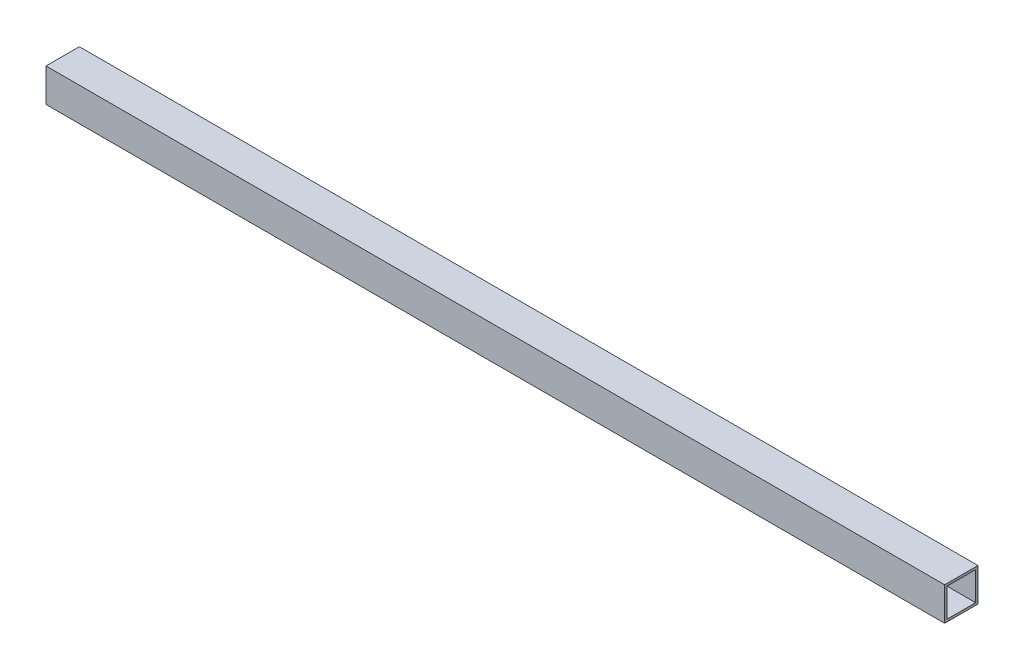
SolidWorks part; units mm, degrees
material "6061 Alloy"
ref_plane "Front Plane" through (0, 0, 0) normal (0, 0, 1) x (1, 0, 0)
ref_plane "Top Plane" through (0, 0, 0) normal (0, 1, 0) x (1, 0, 0)
ref_plane "Right Plane" through (0, 0, 0) normal (1, 0, 0) x (0, 0, -1)
sketch "Sketch1" plane through (0, 0, 0) normal (1, 0, 0) x (0, 0, -1)
  line L1 (0, 0) -> (44.45, 0)
  line L2 (0, 0) -> (0, 44.45)
  line L3 (0, 44.45) -> (44.45, 44.45)
  line L4 (44.45, 0) -> (44.45, 44.45)
  line L5 (3.175, 41.275) -> (41.275, 41.275)
  line L6 (3.175, 41.275) -> (3.175, 3.175)
  line L7 (3.175, 3.175) -> (41.275, 3.175)
  line L8 (41.275, 41.275) -> (41.275, 3.175)
  dimension "D1" = 44.45
  dimension "D2" = 44.45
  dimension "D3" = 3.175
  dimension "D4" = 3.175
  dimension "D5" = 38.1
  dimension "D6" = 38.1
extrude "Boss-Extrude1" add sketch "Sketch1" along normal blind 1196.975
sketch "Sketch2" plane through (0, 0, 0) normal (0, 0, 1) x (1, 0, 0)
  line L0 (0, 44.45) -> (0, 0) construction
  line L1 (1196.975, 44.45) -> (0, 44.45) construction
  circle A0 centre (73.025, 22.225) radius 3.3734
  circle A1 centre (333.375, 22.225) radius 3.3734
  circle A2 centre (593.725, 22.225) radius 3.3734
  circle A3 centre (22.225, 22.225) radius 3.3734
  dimension "D3" = 6.7469
  dimension "D7" = 6.7469
  dimension "D1" = 73.025
  dimension "D2" = 22.225
  dimension "D5" = 520.7
  dimension "D6" = 22.225
  dimension "D8" = 22.225
  dimension "D4" = 3
sketch "Sketch3" plane through (0, 0, 0) normal (0, -1, 0) x (1, 0, 0)
  line L0 (1196.975, -44.45) -> (0, -44.45) construction
  line L1 (0, 0) -> (0, -44.45) construction
  line L2 (1196.975, 0) -> (0, 0) construction
  circle A0 centre (358.775, -22.225) radius 3.3734
  circle A1 centre (22.225, -22.225) radius 3.3734
  dimension "D2" = 6.7469
  dimension "D5" = 22.225
  dimension "D1" = 22.225
  dimension "D3" = 358.775
  dimension "D4" = 336.55
